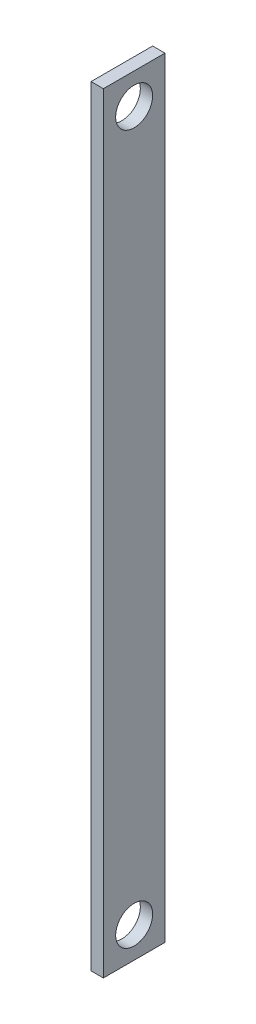
SolidWorks part; units mm, degrees
ref_plane "Front Plane" through (0, 0, 0) normal (0, 0, 1) x (1, 0, 0)
ref_plane "Top Plane" through (0, 0, 0) normal (0, 1, 0) x (1, 0, 0)
ref_plane "Right Plane" through (0, 0, 0) normal (1, 0, 0) x (0, 0, -1)
sketch "Sketch1" plane through (0, 0, 0) normal (1, 0, 0) x (0, 0, -1)
  line L1 (-5, -62.5) -> (5, -62.5)
  line L2 (-5, -62.5) -> (-5, 62.5)
  line L3 (-5, 62.5) -> (5, 62.5)
  line L4 (5, -62.5) -> (5, 62.5)
  line L5 (-5, -62.5) -> (5, 62.5) construction
  line L6 (-5, 62.5) -> (5, -62.5) construction
  point P0 (0, 0)
  dimension "D1" = 10
  dimension "D2" = 125
extrude "Boss-Extrude1" add sketch "Sketch1" along normal blind 2
sketch "Sketch3" plane through (2, 0, 0) normal (1, 0, 0) x (0, 0, -1)
  line L0 (5, 62.5) -> (-5, 62.5) construction
  circle A0 centre (0, 57.5) radius 3
  circle A1 centre (0, -57.5) radius 3
  dimension "D1" = 5
  dimension "D2" = 2
extrude "Cut-Extrude2" cut sketch "Sketch3" against normal up to surface (2 mm away) up to face at (0, 0, 0)
